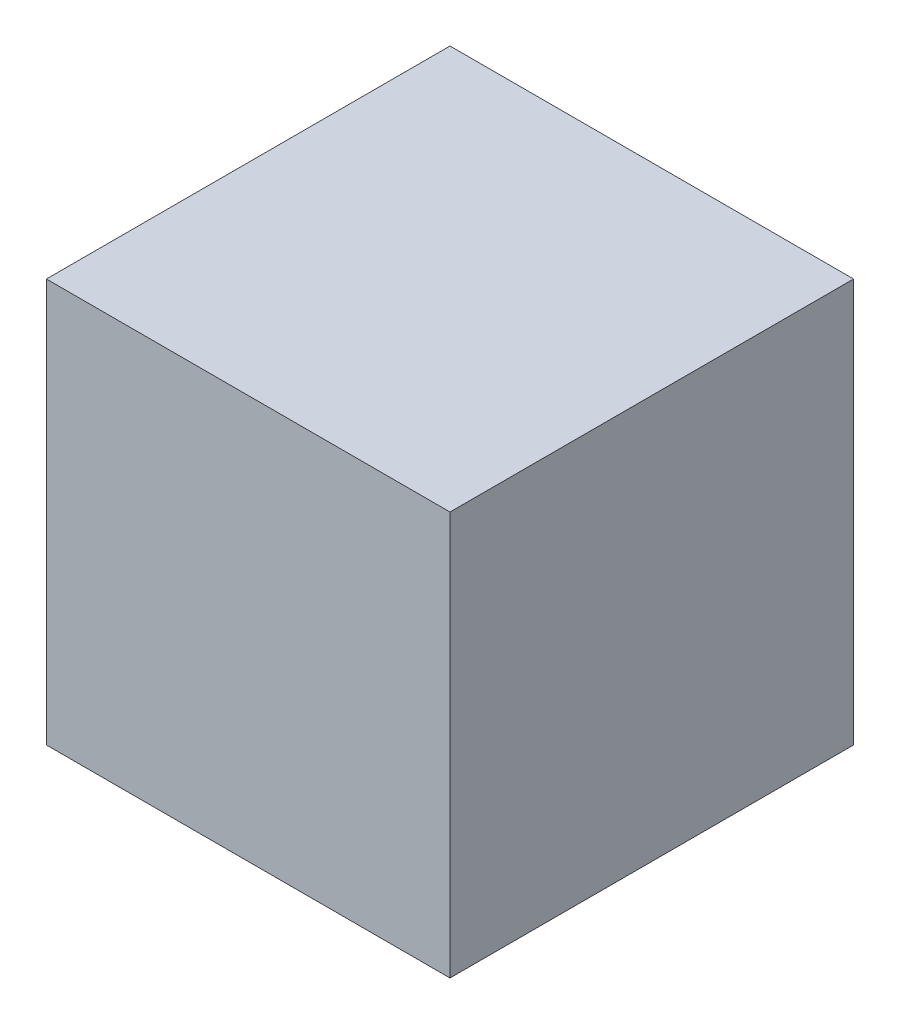
SolidWorks part; units mm, degrees
ref_plane "前视基准面" through (0, 0, 0) normal (0, 0, 1) x (1, 0, 0)
ref_plane "上视基准面" through (0, 0, 0) normal (0, 1, 0) x (1, 0, 0)
ref_plane "右视基准面" through (0, 0, 0) normal (1, 0, 0) x (0, 0, -1)
sketch "草图1" plane through (0, 0, 0) normal (0, 0, 1) x (1, 0, 0)
  line L1 (-17.485, 10.02) -> (22.515, 10.02)
  line L2 (-17.485, 10.02) -> (-17.485, -29.98)
  line L3 (-17.485, -29.98) -> (22.515, -29.98)
  line L4 (22.515, 10.02) -> (22.515, -29.98)
  dimension "D1" = 40
  dimension "D2" = 40
extrude "凸台-拉伸1" add sketch "草图1" along normal blind 40
